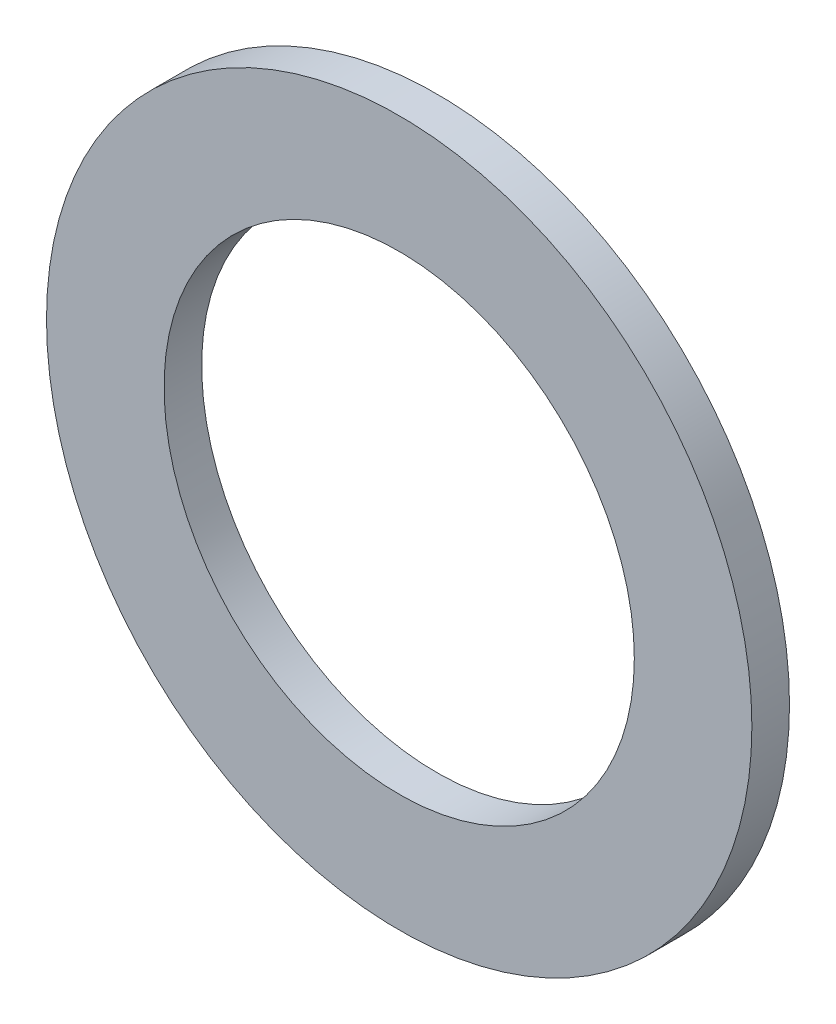
SolidWorks part; units mm, degrees
material "AISI 316 Stainless Steel Sheet (SS)"
ref_plane "Front Plane" through (0, 0, 0) normal (0, 0, 1) x (1, 0, 0)
ref_plane "Top Plane" through (0, 0, 0) normal (0, 1, 0) x (1, 0, 0)
ref_plane "Right Plane" through (0, 0, 0) normal (1, 0, 0) x (0, 0, -1)
sketch "Sketch1" plane through (0, 0, 0) normal (0, 0, 1) x (1, 0, 0)
  line L0 (-2.3812, 0) -> (2.3812, 0) construction
  line L1 (0, -2.3812) -> (0, 2.3812) construction
  circle A0 centre (0, 0) radius 2.3812
  circle A1 centre (0, 0) radius 1.5875
  point P4 (0, 0)
  point P9 (0, 0)
  dimension "ID" = 3.175
  dimension "OD" = 4.7625
sketch "Sketch2" plane through (0, 0, 0) normal (1, 0, 0) x (0, 0, -1)
  line L0 (0.127, 2.3812) -> (-0.127, 2.3812) construction
  line L1 (0, 2.3812) -> (0, -2.3812) construction
  point P4 (0, 2.3812)
  dimension "Thickness" = 0.254
sketch "Sketch3" plane through (0, 0, 0) normal (0, 0, 1) x (1, 0, 0)
  line L0 (0, -2.3812) -> (0, 2.3812) construction
  circle A0 centre (0, 0) radius 2.3812
  circle A1 centre (0, 0) radius 1.5875
  circle A2 centre (0, 0) radius 1.5875 construction
extrude "Boss-Extrude1" add sketch "Sketch3" along normal mid plane 0.254
equation "\"D1@Boss-Extrude1\" = \"Thickness@Sketch2\""
